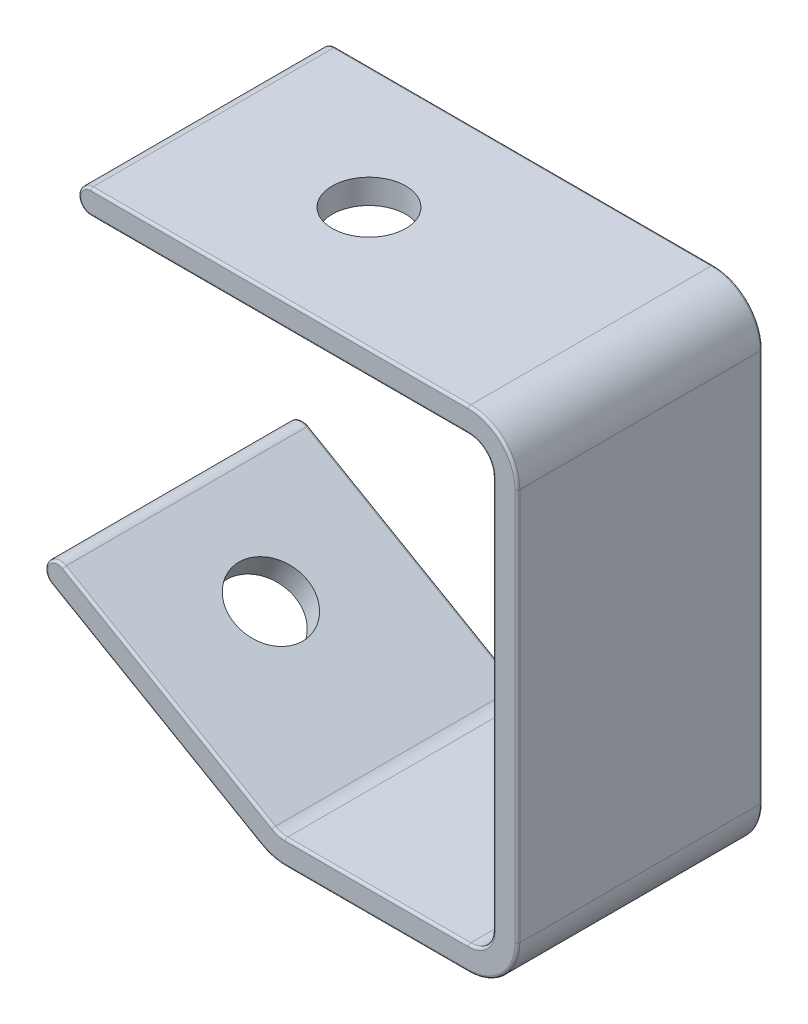
SolidWorks part; units mm, degrees
ref_plane "前视基准面" through (0, 0, 0) normal (0, 0, 1) x (1, 0, 0)
ref_plane "上视基准面" through (0, 0, 0) normal (0, 1, 0) x (1, 0, 0)
ref_plane "右视基准面" through (0, 0, 0) normal (1, 0, 0) x (0, 0, -1)
other "Configuration Table"
sketch "草图1" plane through (0, 0, 0) normal (0, 0, 1) x (1, 0, 0)
  line L0 (0, 10) -> (0, 90)
  line L1 (-10, 100) -> (-87, 100)
  line L2 (-10, 0) -> (-47.3205, 0)
  line L3 (-52.3205, 1.3397) -> (-95, 25.9808)
  line L4 (-49.8205, 5.6699) -> (-92.5, 30.3109)
  line L5 (-10, 5) -> (-47.3205, 5)
  line L6 (-5, 10) -> (-5, 90)
  line L7 (-10, 95) -> (-87, 95)
  arc A0 (0, 90) -> (-10, 100) centre (-10, 90) ccw
  arc A1 (0, 10) -> (-10, 0) centre (-10, 10) cw
  arc A2 (-47.3205, 0) -> (-52.3205, 1.3397) centre (-47.3205, 10) cw
  arc A3 (-47.3205, 5) -> (-49.8205, 5.6699) centre (-47.3205, 10) cw
  arc A4 (-5, 10) -> (-10, 5) centre (-10, 10) cw
  arc A5 (-5, 90) -> (-10, 95) centre (-10, 90) ccw
  arc A6 (-95, 25.9808) -> (-92.5, 30.3109) centre (-93.75, 28.1458) cw
  arc A7 (-87, 100) -> (-87, 95) centre (-87, 97.5) ccw
  point P8 (0, 100)
  point P11 (0, 0)
  point P14 (-50, 0)
  dimension "D6" = 10
  dimension "D1" = 30
  dimension "D2" = 45
  dimension "D3" = 50
  dimension "D4" = 100
  dimension "D5" = 87
  dimension "D7" = 5
extrude "凸台-拉伸1" add sketch "草图1" along normal mid plane 50
sketch "草图2" plane through (0, 0, 0) normal (0, 0, 1) x (1, 0, 0)
  line L0 (-55.2628, 100) -> (-55.2628, 55) construction
  line L1 (-10, 100) -> (-87, 100) construction
  line L2 (-55.2628, 55) -> (-77.7628, 16.0289) construction
  line L3 (-95, 25.9808) -> (-52.3205, 1.3397) construction
  dimension "D1" = 45
  dimension "D2" = 45
sketch "草图3" plane through (-10, -17.3205, 0) normal (0.5, 0.866, 0) x (0.866, -0.5, 0)
  line L0 (-97.859, 0) -> (-75.359, 0) construction
  circle A0 centre (-75.359, 0) radius 7.5
  dimension "D1" = 15
extrude "切除-拉伸1" cut sketch "草图3" against normal blind 5
sketch "草图5" plane through (0, 100, 0) normal (0, 1, 0) x (1, 0, 0)
  line L0 (-55.2628, 0) -> (-77.7628, 0) construction
  circle A0 centre (-55.2628, 0) radius 7.5
  dimension "D1" = 15
extrude "切除-拉伸2" cut sketch "草图5" against normal blind 5
fillet "圆角1" radius 0.5 32 edges at (-48.6146, 5.1704, -25) (-28.6603, 5, -25) (-6.4645, 6.4645, -25) (-5, 50, -25) (-6.4645, 93.5355, -25) (-48.5, 95, -25) (-89.5, 97.5, -25) (-48.5, 100, -25) (-2.9289, 97.0711, -25) (0, 50, -25) (-2.9289, 2.9289, -25) (-28.6603, 0, -25) (-49.9087, 0.3407, -25) (-73.6603, 13.6603, -25) (-95.9151, 29.3958, -25) (-48.6146, 5.1704, 25) (-28.6603, 5, 25) (-6.4645, 6.4645, 25) (-5, 50, 25) (-6.4645, 93.5355, 25) (-48.5, 95, 25) (-89.5, 97.5, 25) (-48.5, 100, 25) (-2.9289, 97.0711, 25) (0, 50, 25) (-2.9289, 2.9289, 25) (-28.6603, 0, 25) (-49.9087, 0.3407, 25) (-73.6603, 13.6603, 25) (-95.9151, 29.3958, 25) (-71.1603, 17.9904, -25) (-71.1603, 17.9904, 25)
